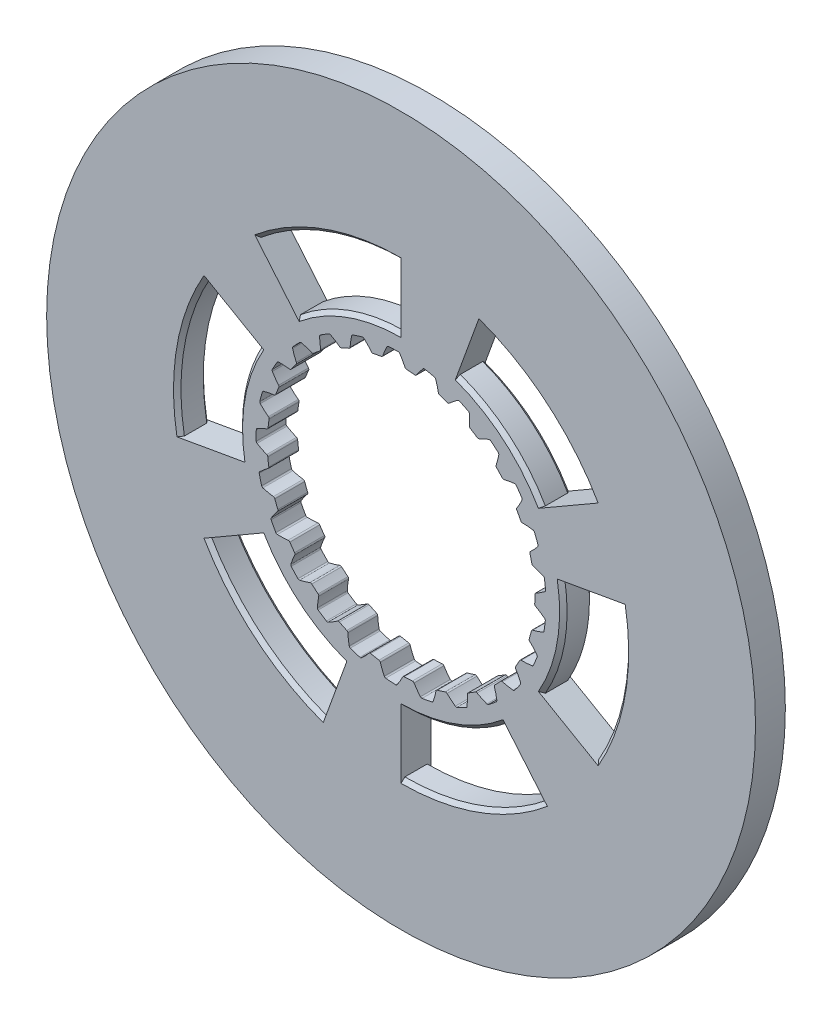
SolidWorks part; units mm, degrees
material "1.6587 (18CrNiMo7-6)"
ref_plane "Front Plane" through (0, 0, 0) normal (0, 0, 1) x (1, 0, 0)
ref_plane "Top Plane" through (0, 0, 0) normal (0, 1, 0) x (1, 0, 0)
ref_plane "Right Plane" through (0, 0, 0) normal (1, 0, 0) x (0, 0, -1)
sketch "Sketch1" plane through (0, 0, 0) normal (0, 0, 1) x (1, 0, 0)
  circle A0 centre (0, 0) radius 35.85
  circle A1 centre (0, 0) radius 95
  dimension "D1" = 71.7
  dimension "D2" = 190
extrude "Boss-Extrude1" add sketch "Sketch1" along normal blind 8
sketch "Sketch2" plane through (0, 0, 8) normal (0, 0, 1) x (1, 0, 0)
  line L0 (0, 0) -> (37.4458, 2.0146) construction
  line L1 (0, 0) -> (45.8703, 5.3719) construction
  circle A0 centre (0, 0) radius 37.5 construction
  arc A1 (35.8337, 1.0823) -> (35.1141, 7.2265) centre (0, 0) ccw
  arc A2 (38.7391, 2.9335) -> (38.3686, 6.0967) centre (0, 0) ccw
  spline S0 degree 4 poles (32.476, 0) (32.4914, 0.0003) (32.5344, 0.0018) (32.6158, 0.0079) (32.7482, 0.0223) (32.9164, 0.0473) (33.1329, 0.0872) (33.3867, 0.1439) (33.6639, 0.2163) (33.9634, 0.3059) (34.2601, 0.4048) (34.554, 0.5124) (34.8448, 0.6274) (35.1945, 0.7761) (35.6099, 0.9672) (36.0896, 1.2091) (36.626, 1.5052) (37.164, 1.8298) (37.6859, 2.1679) (38.2038, 2.5305) (38.6983, 2.8963) (39.2016, 3.2972) (39.6609, 3.6779) (40.1632, 4.1272) (40.5651, 4.4965) (41.0814, 5.0072) (41.3822, 5.3158) (41.7292, 5.685) (41.8807, 5.8532) (41.9741, 5.9566) knots 0 0 0 0 0 0.005377 0.015084 0.028532 0.04661 0.064855 0.092111 0.119476 0.146842 0.174209 0.201575 0.228941 0.256307 0.307035 0.361767 0.4165 0.471232 0.525964 0.580697 0.635429 0.690161 0.744894 0.799626 0.854358 0.909091 0.954545 1 1 1 1 1 construction
  spline S1 degree 4 poles (35.8337, 1.0823) (35.9646, 1.1484) (36.2334, 1.2885) (36.6345, 1.5103) (37.164, 1.8298) (37.6859, 2.1679) (38.1493, 2.4923) (38.4702, 2.7278) (38.667, 2.8779) (38.7391, 2.9335) knots 0.310476 0.310476 0.310476 0.310476 0.310476 0.361767 0.4165 0.471232 0.525964 0.580697 0.612361 0.612361 0.612361 0.612361 0.612361
  spline S2 degree 4 poles (35.1141, 7.2265) (35.2567, 7.1924) (35.5506, 7.1182) (35.9922, 6.9951) (36.5812, 6.8065) (37.167, 6.5982) (37.6928, 6.3896) (38.0595, 6.2347) (38.2857, 6.1342) (38.3686, 6.0967) knots 0.310476 0.310476 0.310476 0.310476 0.310476 0.361767 0.4165 0.471232 0.525964 0.580697 0.612361 0.612361 0.612361 0.612361 0.612361
  dimension "D1" = 75
  dimension "D2" = 71.7
  dimension "D3" = 77.7
  dimension "D4" = 3.6
extrude "Cut-Extrude1" cut sketch "Sketch2" against normal blind 8
fillet "Fillet1" radius 0.48 4 edges at (35.8337, 1.0823, 4) (38.7391, 2.9335, 4) (35.1141, 7.2265, 4) (38.3686, 6.0967, 4)
pattern_circular "CirPattern1" count 25 over 360 about axis through (0, 0, 8) along (0, 0, -1) of "Cut-Extrude1", "Fillet1"
sketch "Sketch3" plane through (0, 0, 8) normal (0, 0, 1) x (1, 0, 0)
  line L0 (0, 0) -> (0, 101.6605)
  line L1 (0, 0) -> (35.4301, 97.3435)
  line L2 (0, 0) -> (102.017, 17.9883)
  line L3 (0, 0) -> (88.0406, 50.8303)
  line L4 (0, 0) -> (66.5869, -79.3551)
  line L5 (0, 0) -> (88.0406, -50.8303)
  line L6 (0, 0) -> (-35.4301, -97.3435)
  line L7 (0, 0) -> (0, -101.6605)
  line L8 (0, 0) -> (-102.017, -17.9883)
  line L9 (0, 0) -> (-88.0406, -50.8303)
  line L10 (0, 0) -> (-66.5869, 79.3551)
  line L11 (0, 0) -> (-88.0406, 50.8303)
  circle A0 centre (0, 0) radius 60
  circle A1 centre (0, 0) radius 43.5
  point P19 (0, 0)
  dimension "D1" = 120
  dimension "D2" = 87
  dimension "D3" = 20
  dimension "D4" = 6
extrude "Cut-Extrude2" cut sketch "Sketch3" against normal blind 8 contours A1 L0 A0 L10 | A1 L11 A0 L8 | A1 L9 A0 L6 | A1 L3 A0 L1 | A1 L5 A0 L2 | A1 L7 A0 L4
chamfer "Chamfer1" distance 1 24 edges at (42.8391, -7.5537, 8) (59.0885, -10.4189, 8) (-27.9613, -33.3229, 8) (20.5212, -56.3816, 8) (-59.0885, 10.4189, 8) (-38.5673, -45.9627, 8) (-27.9613, -33.3229, 0) (-38.5673, -45.9627, 0) (20.5212, -56.3816, 0) (59.0885, -10.4189, 0) (14.8779, -40.8766, 8) (14.8779, -40.8766, 0) (42.8391, -7.5537, 0) (27.9613, 33.3229, 0) (-20.5212, 56.3816, 0) (-59.0885, 10.4189, 0) (-14.8779, 40.8766, 0) (38.5673, 45.9627, 0) (38.5673, 45.9627, 8) (27.9613, 33.3229, 8) (-42.8391, 7.5537, 0) (-42.8391, 7.5537, 8) (-20.5212, 56.3816, 8) (-14.8779, 40.8766, 8)
